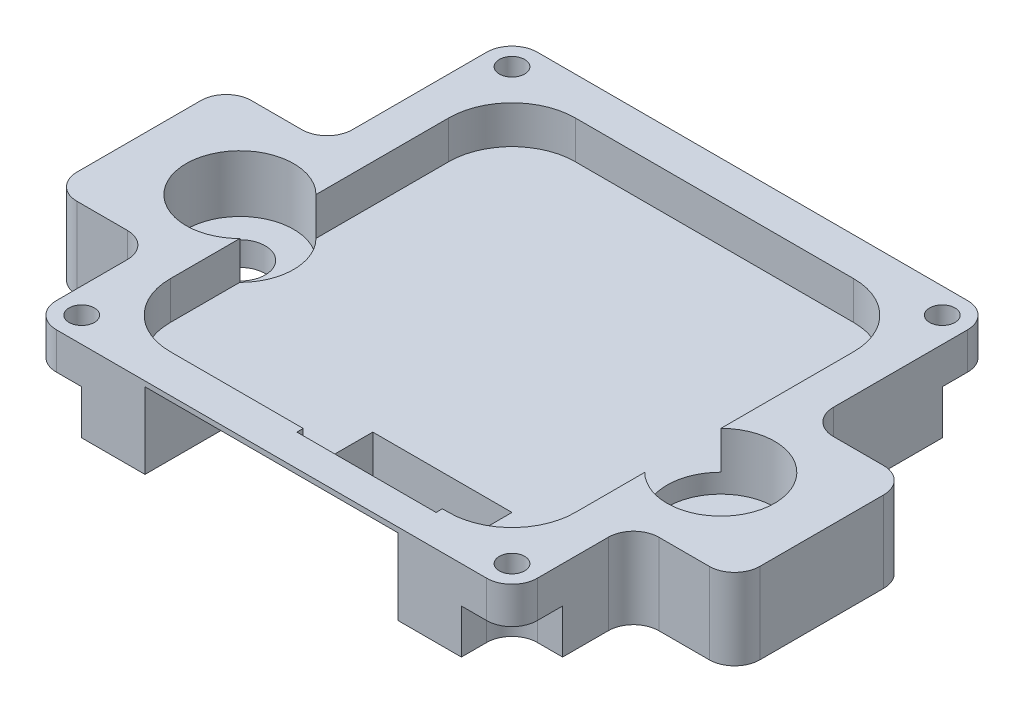
SolidWorks part; units mm, degrees
ref_plane "Front Plane" through (0, 0, 0) normal (0, 0, 1) x (1, 0, 0)
ref_plane "Top Plane" through (0, 0, 0) normal (0, 1, 0) x (1, 0, 0)
ref_plane "Right Plane" through (0, 0, 0) normal (1, 0, 0) x (0, 0, -1)
sketch "Sketch1" plane through (0, 0, 0) normal (0, 1, 0) x (1, 0, 0)
  line L0 (-55, 0) -> (55, 0) construction
  line L1 (-26.982, -6.8935) -> (26.982, -6.8935)
  line L2 (-26.982, -6.8935) -> (-26.982, 6.8935)
  line L3 (-26.982, 6.8935) -> (26.982, 6.8935)
  line L4 (26.982, -6.8935) -> (26.982, 6.8935)
  line L5 (-26.982, -6.8935) -> (26.982, 6.8935) construction
  line L6 (-26.982, 6.8935) -> (26.982, -6.8935) construction
  line L7 (0, 0) -> (0, 6.8935) construction
  circle A0 centre (-19, 0) radius 2
  circle A1 centre (19, 0) radius 2
  point P0 (0, 0)
  dimension "D1" = 4
  dimension "D2" = 38
extrude "Boss-Extrude1" add sketch "Sketch1" along normal blind 6.4
sketch "Sketch3" plane through (0, 6.4, 0) normal (0, 1, 0) x (1, 0, 0)
  line L0 (19, 2) -> (19, 21.5)
  line L1 (-19, -16.5) -> (19, -16.5)
  line L2 (-19, -16.5) -> (-19, -2)
  line L3 (-19, 21.5) -> (19, 21.5)
  line L4 (19, -16.5) -> (19, -2)
  line L5 (-19, -16.5) -> (19, 21.5) construction
  line L6 (-19, 21.5) -> (19, -16.5) construction
  line L7 (-19, 2) -> (-19, 21.5)
  line L8 (0, 0) -> (0, 21.5) construction
  line L10 (0, -3.52) -> (0, 3.52) construction
  arc A0 (-19, 2) -> (-19, -2) centre (-19, 0) cw
  circle A1 centre (-19, 0) radius 2 construction
  arc A2 (19, 2) -> (19, -2) centre (19, 0) ccw
  circle A3 centre (19, 0) radius 2 construction
  circle A4 centre (-17, 19.5) radius 1
  circle A5 centre (17, 19.5) radius 1
  circle A6 centre (-17, -14.5) radius 1
  circle A7 centre (17, -14.5) radius 1
  point P0 (0, 2.5)
  point P21 (0, -3.4204)
  point P24 (0, 0)
  point P25 (19, 21.5)
  point P28 (0.4297, 1.9533)
  point P29 (0.5595, 0.9978)
  point P30 (-1.3932, 1.9934)
  point P31 (0, 0)
  point P34 (0, -2.4464)
  point P35 (0, 0)
  dimension "D4" = 2
  dimension "D1" = 38
  dimension "D2" = 38
  dimension "D3" = 2
  dimension "D5" = 16.5
extrude "Boss-Extrude2" add sketch "Sketch3" against normal up to surface (6.4 mm away) up to face at (-19, 0, 2)
sketch "Sketch4" plane through (0, 6.4, 0) normal (0, 1, 0) x (1, 0, 0)
  circle A0 centre (-19, 0) radius 4.25
  circle A1 centre (19, 0) radius 4.25
  dimension "D1" = 8.5
extrude "Cut-Extrude1" cut sketch "Sketch4" against normal blind 4.5
sketch "Sketch5" plane through (0, 6.4, 0) normal (0, 1, 0) x (1, 0, 0)
  line L0 (19, -16.5) -> (19, -6.8935) construction
  line L1 (-0.5, -14) -> (10.5, -14)
  line L2 (-0.5, -14) -> (-0.5, -8)
  line L3 (-0.5, -8) -> (10.5, -8)
  line L4 (10.5, -14) -> (10.5, -8)
  line L5 (-0.5, -14) -> (10.5, -8) construction
  line L6 (-0.5, -8) -> (10.5, -14) construction
  line L7 (-19, -16.5) -> (19, -16.5) construction
  point P0 (5, -11)
  point P7 (10.5, -11)
  dimension "D1" = 8.5
  dimension "D2" = 2.5
  dimension "D3" = 11
  dimension "D4" = 6
extrude "Cut-Extrude2" cut sketch "Sketch5" against normal through all
sketch "Sketch6" plane through (0, 6.4, 0) normal (0, 1, 0) x (1, 0, 0)
  line L0 (19, 21.5) -> (-19, 21.5) construction
  line L1 (-16, -13.5) -> (16, -13.5)
  line L2 (-16, -13.5) -> (-16, 18.5)
  line L3 (-16, 18.5) -> (16, 18.5)
  line L4 (16, -13.5) -> (16, 18.5)
  line L5 (-16, -13.5) -> (16, 18.5) construction
  line L6 (-16, 18.5) -> (16, -13.5) construction
  line L7 (19, 6.8935) -> (19, 21.5) construction
  line L9 (-19, -6.8935) -> (-19, -16.5) construction
  line L10 (-19, -16.5) -> (19, -16.5) construction
  point P0 (0, 2.5)
  point P10 (0, 0)
  point P11 (-13.7363, -10.8645)
  dimension "D1" = 3
  dimension "D2" = 3
  dimension "D3" = 3
  dimension "D4" = 3
extrude "Cut-Extrude3" cut sketch "Sketch6" against normal blind 3
fillet "Fillet2" radius 2 12 edges at (-19, 3.2, 16.5) (19, 3.2, 16.5) (19, 3.2, 6.8935) (26.982, 3.2, 6.8935) (26.982, 3.2, -6.8935) (19, 3.2, -6.8935) (19, 3.2, -21.5) (-19, 3.2, -21.5) (-19, 3.2, -6.8935) (-26.982, 3.2, -6.8935) (-26.982, 3.2, 6.8935) (-19, 3.2, 6.8935)
fillet "Fillet3" radius 5 4 edges at (-16, 4.9, -18.5) (-16, 4.9, 13.5) (16, 4.9, 13.5) (16, 4.9, -18.5)
sketch "Sketch7" plane through (0, 0, 0) normal (0, -1, 0) x (1, 0, 0)
  line L1 (-17, 16.5) -> (17, 16.5) construction
  line L4 (-17, -17.5) -> (-19, -17.5)
  line L7 (0, 0) -> (0, 16.5) construction
  line L8 (0, 0) -> (26.982, 0) construction
  line L9 (26.982, 4.8935) -> (26.982, -4.8935) construction
  line L25 (-19, -17.5) -> (-19, -21.5)
  line L26 (15, -19.5) -> (15, -21.5)
  line L27 (-17, 12.5) -> (-19, 12.5)
  line L28 (-19, 8.8935) -> (-19, 14.5) construction
  line L29 (-15, 14.5) -> (-15, 16.5)
  line L30 (-15, 16.5) -> (-19, 16.5)
  line L31 (-19, 16.5) -> (-19, 12.5)
  line L32 (15, -21.5) -> (19, -21.5)
  line L33 (19, 14.5) -> (19, 8.8935) construction
  line L34 (17, -21.5) -> (-17, -21.5) construction
  line L35 (19, -8.8935) -> (19, -19.5) construction
  line L36 (-19, -19.5) -> (-19, -8.8935) construction
  line L37 (-15, -19.5) -> (-15, -21.5)
  line L38 (-15, -21.5) -> (-19, -21.5)
  line L39 (19, -17.5) -> (19, -21.5)
  line L40 (19, -17.5) -> (17, -17.5)
  line L41 (17, 12.5) -> (19, 12.5)
  line L42 (19, 12.5) -> (19, 16.5)
  line L43 (15, 16.5) -> (19, 16.5)
  line L44 (15, 16.5) -> (15, 14.5)
  arc A7 (-17, 12.5) -> (-15, 14.5) centre (-17, 14.5) ccw
  arc A8 (-15, -19.5) -> (-17, -17.5) centre (-17, -19.5) ccw
  arc A9 (17, -17.5) -> (15, -19.5) centre (17, -19.5) ccw
  arc A10 (15, 14.5) -> (17, 12.5) centre (17, 14.5) ccw
  dimension "D1" = 2
extrude "Cut-Extrude4" cut sketch "Sketch7" against normal blind 3.5
sketch "Sketch8" plane through (0, 0, 0) normal (1, 0, 0) x (0, 0, -1)
  line L0 (-10, 0) -> (-16.5, 6)
  line L2 (-16.5, 3.5) -> (-16.5, 0) construction
  line L3 (-12.5, 0) -> (-8.8935, 0) construction
  line L4 (-16.5, 6) -> (-16.5, 0)
  line L5 (-16.5, 0) -> (-10, 0)
  point P2 (-13.0617, 0)
  dimension "D1" = 6.5
  dimension "D2" = 6
extrude "Cut-Extrude5" cut sketch "Sketch8" against normal mid plane 20
